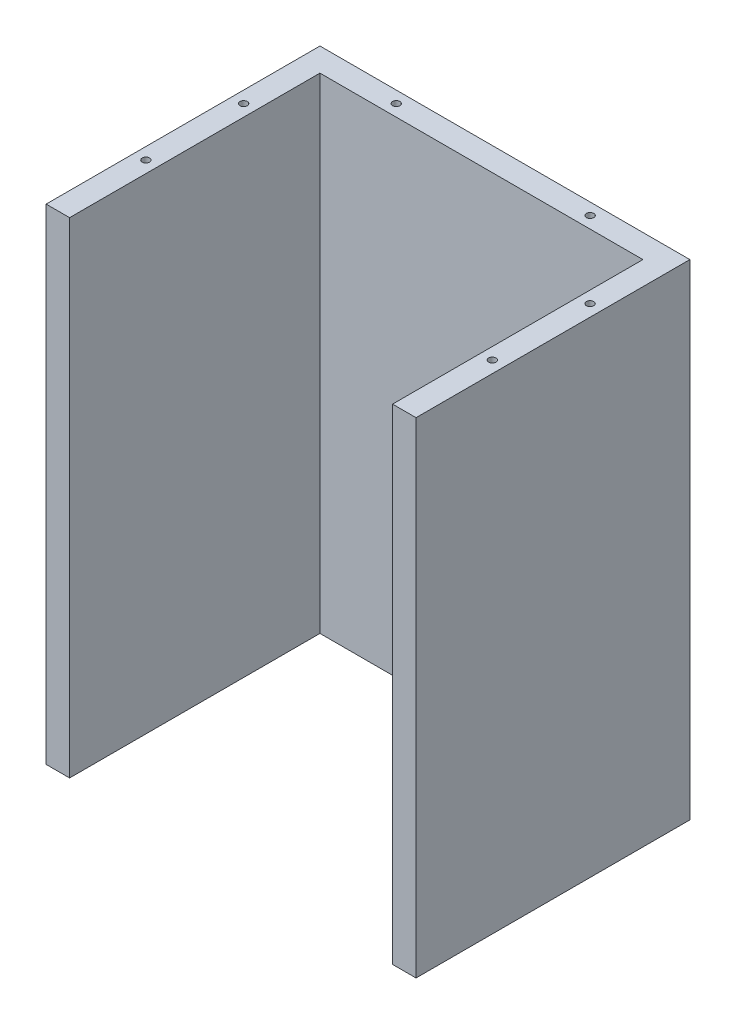
SolidWorks part; units mm, degrees
ref_plane "Front Plane" through (0, 0, 0) normal (0, 0, 1) x (1, 0, 0)
ref_plane "Top Plane" through (0, 0, 0) normal (0, 1, 0) x (1, 0, 0)
ref_plane "Right Plane" through (0, 0, 0) normal (1, 0, 0) x (0, 0, -1)
sketch "Sketch1" plane through (0, 0, 0) normal (0, 1, 0) x (1, 0, 0)
  line L1 (-90.043, -82.55) -> (90.043, -82.55)
  line L2 (-90.043, -82.55) -> (-90.043, 82.55)
  line L3 (-90.043, 82.55) -> (90.043, 82.55)
  line L4 (90.043, -82.55) -> (90.043, 82.55)
  line L5 (-90.043, -82.55) -> (90.043, 82.55) construction
  line L6 (-90.043, 82.55) -> (90.043, -82.55) construction
  point P0 (0, 0)
  dimension "D1" = 165.1
  dimension "D2" = 180.086
extrude "Boss-Extrude1" add sketch "Sketch1" along normal blind 3.302
hole_wizard "M5 Clearance Hole2" positions "Sketch10" profile "Sketch11" hole size "M5" standard "ANSI Metric" end condition up to next
sketch "Sketch10" plane through (0, 3.302, 0) normal (0, 1, 0) x (1, 0, 0)
  line L0 (-90.043, -82.55) -> (90.043, -82.55) construction
  line L1 (90.043, -82.55) -> (90.043, 82.55) construction
  line L2 (-90.043, 82.55) -> (-90.043, -82.55) construction
  line L3 (90.043, 82.55) -> (-90.043, 82.55) construction
  point P0 (51.943, -72.39)
  point P7 (-51.943, -72.39)
  point P9 (51.943, 72.39)
  point P16 (-51.943, 72.39)
  dimension "D1" = 10.16
  dimension "D2" = 38.1
  dimension "D3" = 10.16
  dimension "D4" = 38.1
  dimension "D5" = 10.16
sketch "Sketch11" plane through (51.943, 3.302, 72.39) normal (1, 0, 0) x (0, 0, 1)
  line L0 (0, 0) -> (0, 3.302)
  line L1 (0, 3.302) -> (2.75, 3.302)
  line L2 (2.75, 3.302) -> (2.75, 0)
  line L5 (2.75, 0) -> (0, 0)
  line L11 (0, -6.35) -> (0, 107.95) construction
  dimension "Thru Hole Dia." = 5.5
  dimension "Thru Hole Depth" = 3.302
sketch "Sketch12" plane through (0, 0, 0) normal (0, -1, 0) x (1, 0, 0)
  line L0 (0, 82.55) -> (0, 59.25) construction
  line L1 (-90.043, 82.55) -> (90.043, 82.55) construction
  line L2 (-90.043, 0) -> (-70.043, 0) construction
  line L3 (-90.043, -82.55) -> (-90.043, 82.55) construction
  line L4 (0, -82.55) -> (0, -59.25) construction
  line L5 (90.043, -82.55) -> (-90.043, -82.55) construction
  line L11 (90.043, 82.55) -> (90.043, -82.55) construction
  line L12 (90.043, 59.25) -> (-70.043, 59.25)
  line L13 (90.043, 59.25) -> (90.043, -59.25)
  line L14 (90.043, -59.25) -> (-70.043, -59.25)
  line L15 (-70.043, 59.25) -> (-70.043, -59.25)
  line L16 (-70.043, 59.25) -> (-59.883, 59.25)
  line L17 (90.043, 59.25) -> (79.883, 59.25)
  line L18 (-59.883, -59.25) -> (-59.883, -49.09) construction
  line L19 (79.883, -59.25) -> (79.883, -49.09) construction
  line L20 (-59.883, 59.25) -> (-59.883, -49.09)
  line L21 (-59.883, -49.09) -> (79.883, -49.09)
  line L22 (79.883, -49.09) -> (79.883, 59.25)
  line M13 (90.043, -82.55) -> (90.043, 82.55)
fillet "Fillet1" radius 3.302 4 edges at (-90.043, 1.651, -82.55) (90.043, 1.651, -82.55) (90.043, 1.651, 82.55) (-90.043, 1.651, 82.55)
extrude "Boss-Extrude2" add sketch "Sketch12" along normal blind 210 contours L22 L21 L20 L12 L15 L14 M13
sketch "Sketch21" plane through (0, -210, 0) normal (0, -1, 0) x (1, 0, 0)
  line L0 (-64.963, 59.25) -> (-64.963, -59.25) construction
  line L1 (-59.883, 59.25) -> (-70.043, 59.25) construction
  line L2 (90.043, -59.25) -> (-70.043, -59.25) construction
  line L3 (84.963, 59.25) -> (84.963, -59.25) construction
  line L4 (90.043, 59.25) -> (79.883, 59.25) construction
  line L5 (90.043, -59.25) -> (-70.043, -59.25) construction
  line L6 (-70.043, -59.25) -> (-70.043, -54.17) construction
  line L7 (-70.043, 59.25) -> (-70.043, -59.25) construction
  line L8 (-70.043, -54.17) -> (90.043, -54.17) construction
  line L9 (90.043, -59.25) -> (90.043, 59.25) construction
hole_wizard "1/8 (0.1250) Dowel Hole1" positions "Sketch22" profile "Sketch24" hole size "1/8" standard "ANSI Inch"
sketch "Sketch22" plane through (0, -210, 0) normal (0, -1, 0) x (-1, 0, 0)
  line L0 (64.963, -59.25) -> (64.963, 59.25) construction
  line L1 (70.043, 54.17) -> (-90.043, 54.17) construction
  line L2 (-84.963, -59.25) -> (-84.963, 59.25) construction
  point P0 (64.963, -21.15)
  point P4 (64.963, 21.15)
  point P6 (31.943, 54.17)
  point P10 (-51.943, 54.17)
  point P12 (-84.963, 21.15)
  point P16 (-84.963, -21.15)
  dimension "D1" = 38.1
  dimension "D2" = 38.1
  dimension "D3" = 38.1
  dimension "D4" = 38.1
  dimension "D5" = 38.1
  dimension "D6" = 38.1
sketch "Sketch24" plane through (-64.963, -210, 21.15) normal (1, 0, 0) x (0, 0, -1)
  line L0 (0, 0) -> (0, 26.3539)
  line L1 (0, 26.3539) -> (1.5875, 25.4)
  line L2 (1.5875, 25.4) -> (1.5875, 0)
  line L5 (1.5875, 0) -> (0, 0)
  line L10 (0, 26.3539) -> (-1.5875, 25.4) construction
  line L11 (0, -6.35) -> (0, 107.95) construction
  dimension "Hole Dia." = 3.175
  dimension "Hole Depth" = 25.4
  dimension "Drill Angle" = 118
mirror "Mirror1" about plane through (0, -210, 0) normal (0, -1, 0) of bodies 111
sketch "Sketch25" plane through (0, 3.302, 0) normal (0, 1, 0) x (1, 0, 0)
  line L1 (-100.9417, 87.2377) -> (101.1645, 87.2377)
  line L2 (-100.9417, 87.2377) -> (-100.9417, -90.3573)
  line L3 (-100.9417, -90.3573) -> (101.1645, -90.3573)
  line L4 (101.1645, 87.2377) -> (101.1645, -90.3573)
extrude "Cut-Extrude1" cut sketch "Sketch25" against normal blind 213.3
sketch "Sketch26" plane through (0, -423.302, 0) normal (0, -1, 0) x (1, 0, 0)
  line L1 (-94.7024, 86.792) -> (94.7024, 86.792)
  line L2 (-94.7024, 86.792) -> (-94.7024, -87.2377)
  line L3 (-94.7024, -87.2377) -> (94.7024, -87.2377)
  line L4 (94.7024, 86.792) -> (94.7024, -87.2377)
extrude "Cut-Extrude3" cut sketch "Sketch26" against normal blind 3.302
